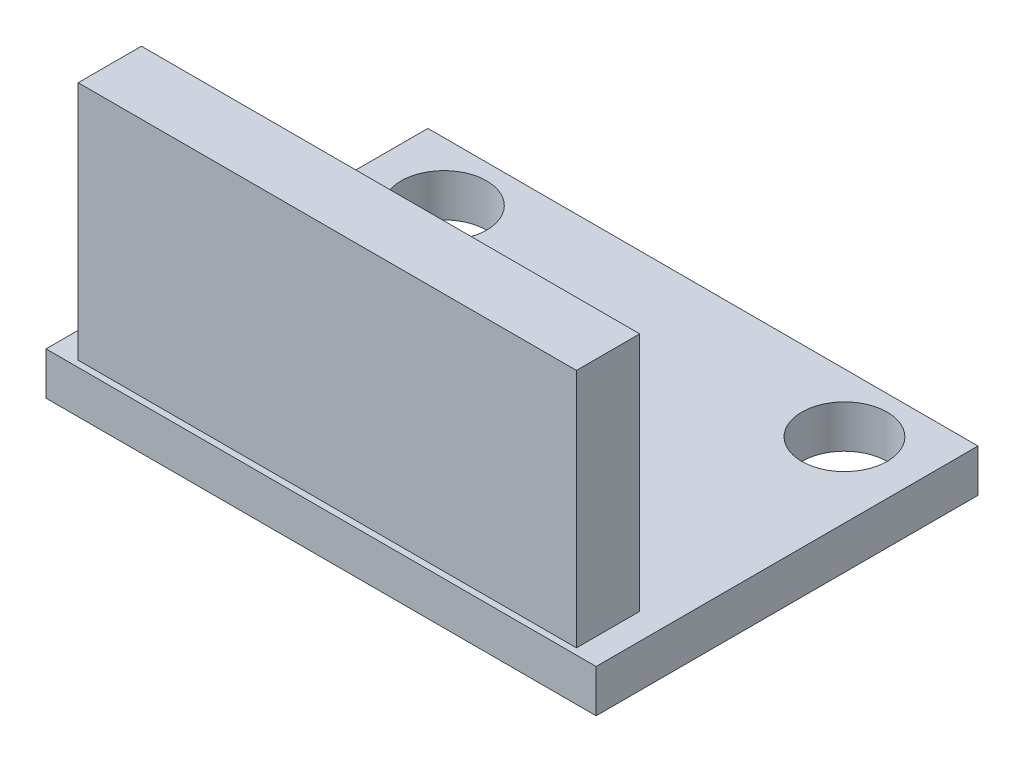
SolidWorks part; units mm, degrees
ref_plane "Front Plane" through (0, 0, 0) normal (0, 0, 1) x (1, 0, 0)
ref_plane "Top Plane" through (0, 0, 0) normal (0, 1, 0) x (1, 0, 0)
ref_plane "Right Plane" through (0, 0, 0) normal (1, 0, 0) x (0, 0, -1)
sketch "Sketch1" plane through (0, 0, 0) normal (0, 1, 0) x (1, 0, 0)
  line L0 (0, 7.15) -> (0, 4.95) construction
  line L1 (-10.3, -7.15) -> (10.3, -7.15)
  line L2 (-10.3, -7.15) -> (-10.3, 7.15)
  line L3 (-10.3, 7.15) -> (10.3, 7.15)
  line L4 (10.3, -7.15) -> (10.3, 7.15)
  line L5 (-10.3, -7.15) -> (10.3, 7.15) construction
  line L6 (-10.3, 7.15) -> (10.3, -7.15) construction
  line L7 (0, 4.95) -> (7.5, 4.95) construction
  line L8 (0, 4.95) -> (-7.5, 4.95) construction
  circle A0 centre (-7.5, 4.95) radius 1.6
  circle A1 centre (7.5, 4.95) radius 1.6
  point P0 (0, 0)
  dimension "D5" = 3.2
  dimension "D1" = 20.6
  dimension "D2" = 14.3
  dimension "D3" = 15
  dimension "D4" = 2.2
extrude "Boss-Extrude1" add sketch "Sketch1" along normal blind 1.6
sketch "Sketch2" plane through (0, 1.6, 0) normal (0, 1, 0) x (1, 0, 0)
  line L1 (-9.329, -4.5472) -> (9.329, -4.5472)
  line L2 (-9.329, -4.5472) -> (-9.329, -6.9158)
  line L3 (-9.329, -6.9158) -> (9.329, -6.9158)
  line L4 (9.329, -4.5472) -> (9.329, -6.9158)
  line L5 (-9.329, -4.5472) -> (9.329, -6.9158) construction
  line L6 (-9.329, -6.9158) -> (9.329, -4.5472) construction
  point P0 (0, -5.7315)
extrude "Boss-Extrude2" add sketch "Sketch2" along normal blind 9
